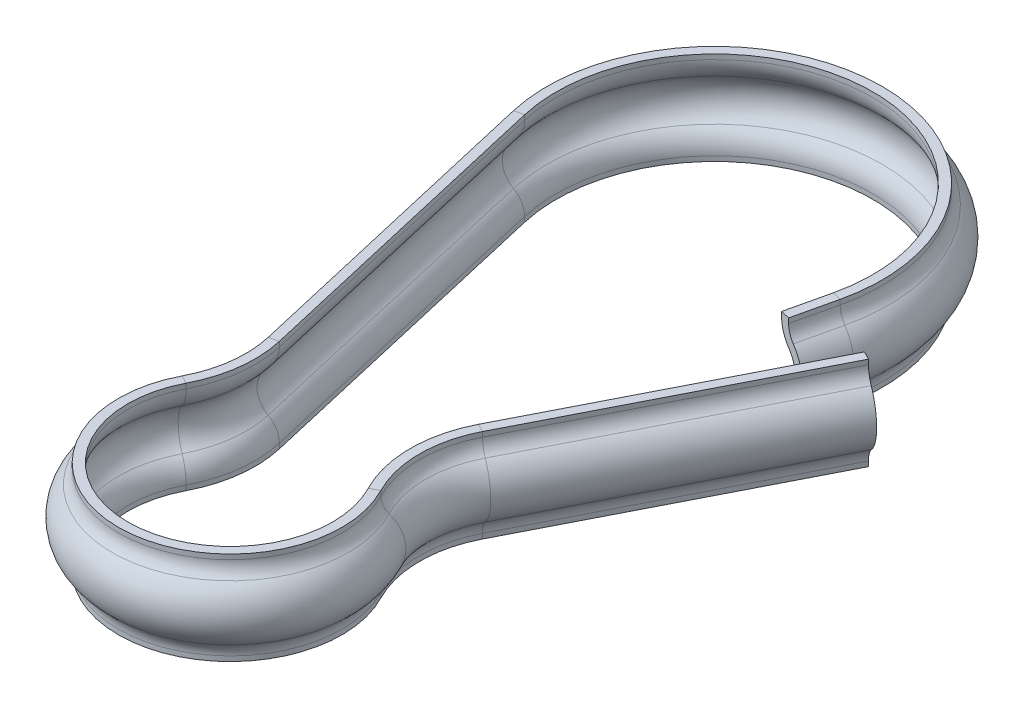
SolidWorks part; units mm, degrees
ref_plane "Front Plane" through (0, 0, 0) normal (0, 0, 1) x (1, 0, 0)
ref_plane "Top Plane" through (0, 0, 0) normal (0, 1, 0) x (1, 0, 0)
ref_plane "Right Plane" through (0, 0, 0) normal (1, 0, 0) x (0, 0, -1)
sketch "Sketch1" plane through (0, 0, 0) normal (0, 1, 0) x (1, 0, 0)
  line L0 (0, 0) -> (0, 26) construction
  line L1 (-9.7437, 23.7505) -> (-5.791, 6.6296)
  line L2 (9.7437, 23.7505) -> (9.2241, 21.5)
  line L3 (6.2078, 7.7748) -> (13.2012, 21.5)
  line L4 (13.2012, 21.5) -> (4.22, 21.5) construction
  arc A0 (-6.22, 3.2111) -> (6.22, 3.2111) centre (0, 0) ccw
  arc A2 (9.7437, 23.7505) -> (-9.7437, 23.7505) centre (0, 26) ccw
  arc A3 (6.2078, 7.7748) -> (6.22, 3.2111) centre (10.6629, 5.5048) ccw
  arc A4 (-5.791, 6.6296) -> (-6.22, 3.2111) centre (-10.6629, 5.5048) cw
  dimension "D1" = 14
  dimension "D2" = 20
  dimension "D3" = 26
  dimension "D5" = 10
  dimension "D4" = 26
  dimension "D6" = 4.5
  dimension "D7" = 14
ref_plane "Plane2" through (13.2012, 0, -21.5) normal (0.454, 0, -0.891) x (-0.891, 0, -0.454)
sketch "Sketch3" plane through (13.2012, 0, -21.5) normal (0.454, 0, -0.891) x (-0.891, 0, -0.454)
  line L0 (0, 0) -> (0, 4.7932) construction
  line L1 (1, -2.5) -> (1, -2.2361)
  line L2 (0, 0) -> (-1.7205, 0) construction
  line L3 (1, 2.2361) -> (1, 2.5)
  line L4 (1.5, -2.5) -> (1.5, -2.2361)
  line L5 (1.5, 2.2361) -> (1.5, 2.5)
  line L6 (1, -2.5) -> (1.5, -2.5)
  line L7 (1, 2.5) -> (1.5, 2.5)
  arc A0 (0.6667, 1.4907) -> (0.6667, -1.4907) centre (2, 0) ccw
  arc A1 (1, -2.2361) -> (0.6667, -1.4907) centre (0, -2.2361) ccw
  arc A2 (1, 2.2361) -> (0.6667, 1.4907) centre (0, 2.2361) cw
  arc A3 (1.5, -2.2361) -> (1, -1.118) centre (0, -2.2361) ccw
  arc A4 (1, 1.118) -> (1, -1.118) centre (2, 0) ccw
  arc A5 (1.5, 2.2361) -> (1, 1.118) centre (0, 2.2361) cw
  point P1 (0, 0)
  dimension "D1" = 4
  dimension "D3" = 2
  dimension "D2" = 1
  dimension "D4" = 5
  dimension "D5" = 0.5
sweep "Sweep1" add profiles "Sketch3" path "Sketch1"
